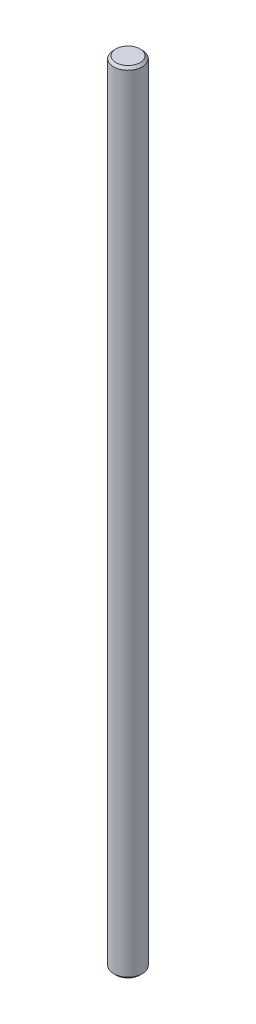
SolidWorks part; units mm, degrees
material "Acier non allié"
ref_plane "Plan de face" through (0, 0, 0) normal (0, 0, 1) x (1, 0, 0)
ref_plane "Plan de dessus" through (0, 0, 0) normal (0, 1, 0) x (1, 0, 0)
ref_plane "Plan de droite" through (0, 0, 0) normal (1, 0, 0) x (0, 0, -1)
sketch "Sketch1" plane through (0, 0, 0) normal (0, 1, 0) x (1, 0, 0)
  circle A0 centre (0, 0.0104) radius 6
  dimension "D1" = 12
extrude "Extrude1" add sketch "Sketch1" along normal blind 330
chamfer "Chamfer1" distance 1 angle 45 2 edges at (0, 0, 5.9896) (0, 330, 5.9896)
